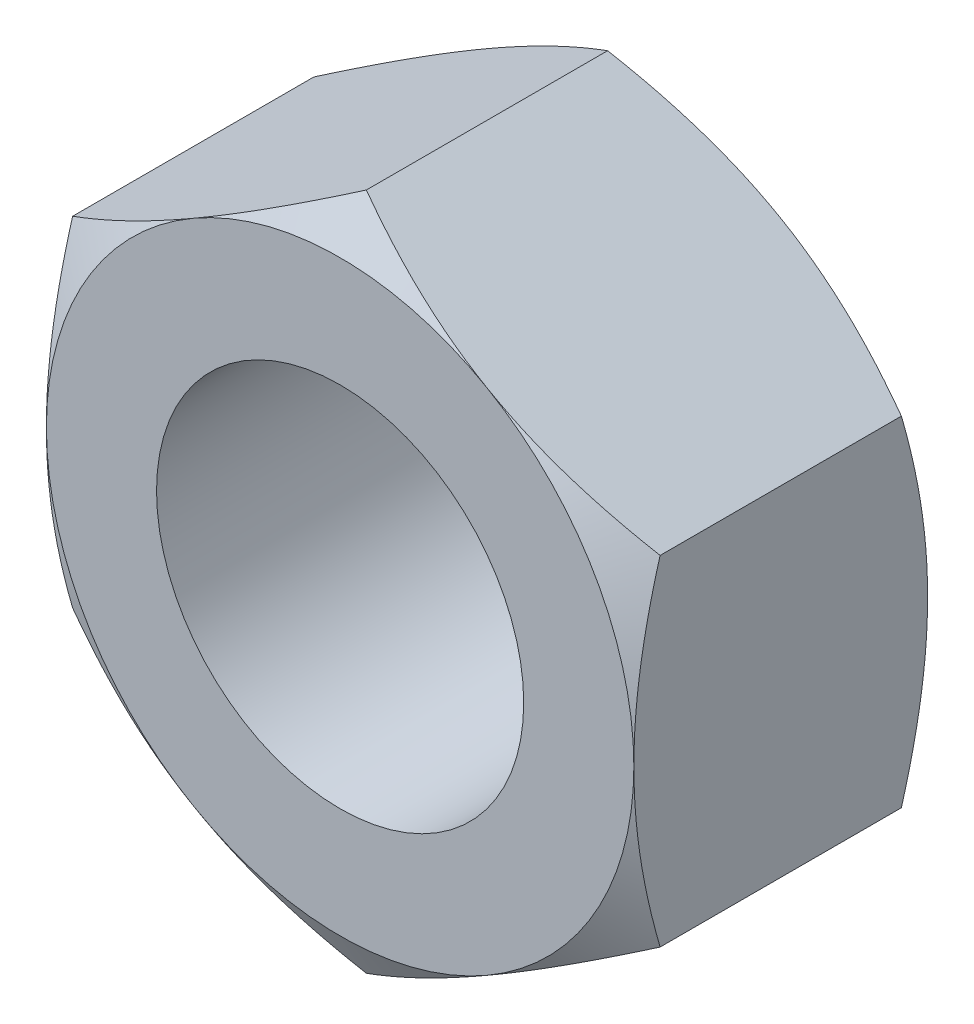
SolidWorks part; units mm, degrees
ref_plane "Front Plane" through (0, 0, 0) normal (0, 0, 1) x (1, 0, 0)
ref_plane "Top Plane" through (0, 0, 0) normal (0, 1, 0) x (1, 0, 0)
ref_plane "Right Plane" through (0, 0, 0) normal (1, 0, 0) x (0, 0, -1)
sketch "Sketch1" plane through (0, 0, 0) normal (0, 0, 1) x (1, 0, 0)
  line L1 (0, -2.3094) -> (2, -1.1547)
  line L2 (2, -1.1547) -> (2, 1.1547)
  line L3 (2, 1.1547) -> (0, 2.3094)
  line L4 (0, 2.3094) -> (-2, 1.1547)
  line L5 (-2, 1.1547) -> (-2, -1.1547)
  line L6 (-2, -1.1547) -> (0, -2.3094)
  circle A0 centre (0, 0) radius 1.25
  circle A1 centre (0, 0) radius 2 construction
  dimension "D1" = 4
  dimension "D2" = 2.5
extrude "Boss-Extrude1" add sketch "Sketch1" along normal blind 2
cosmetic thread "Cosmetic Thread1" parameters "D2"=4
sketch "Sketch2" plane through (0, 0, 2) normal (0, 0, 1) x (1, 0, 0)
  circle A0 centre (0, 0) radius 2 construction
  circle A1 centre (0, 0) radius 2
extrude "Cut-Extrude1" cut sketch "Sketch2" against normal blind 2 draft 60 flip side to cut
sketch "Sketch3" plane through (0, 0, 0) normal (0, 0, -1) x (-1, 0, 0)
  circle A0 centre (0, 0) radius 2 construction
  circle A1 centre (0, 0) radius 2
extrude "Cut-Extrude2" cut sketch "Sketch3" against normal blind 2 draft 60 flip side to cut
